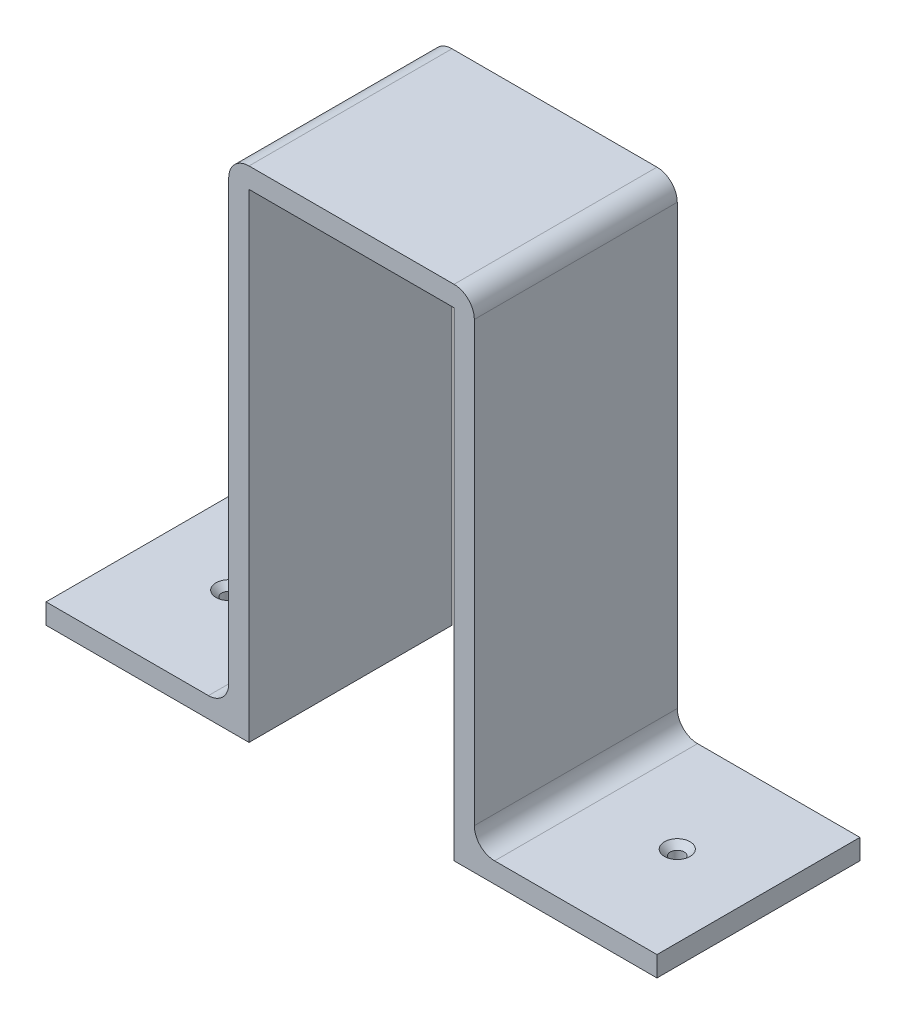
SolidWorks part; units mm, degrees
ref_plane "Plan de face" through (0, 0, 0) normal (0, 0, 1) x (1, 0, 0)
ref_plane "Plan de dessus" through (0, 0, 0) normal (0, 1, 0) x (1, 0, 0)
ref_plane "Plan de droite" through (0, 0, 0) normal (1, 0, 0) x (0, 0, -1)
sketch "Esquisse1" plane through (0, 0, 0) normal (0, 0, 1) x (1, 0, 0)
  line L0 (-25.25, 0) -> (25.25, 0)
  line L1 (-25.25, 0) -> (-25.25, -118)
  line L2 (-25.25, -118) -> (-75.25, -118)
  line L3 (0, -55) -> (0, 55) construction
  line L4 (25.25, 0) -> (25.25, -118)
  line L5 (25.25, -118) -> (75.25, -118)
  line L6 (-30.25, -113) -> (-75.25, -113)
  line L7 (-30.25, 5) -> (-30.25, -113)
  line L8 (-30.25, 5) -> (30.25, 5)
  line L9 (30.25, 5) -> (30.25, -113)
  line L10 (30.25, -113) -> (75.25, -113)
  line L11 (-75.25, -118) -> (-75.25, -113)
  line L12 (75.25, -118) -> (75.25, -113)
  point P4 (0, 0)
  dimension "D1" = 50.5
  dimension "D2" = 118
  dimension "D4" = 50
  dimension "D3" = 5
extrude "Boss.-Extru.1" add sketch "Esquisse1" along normal blind 50
fillet "Congé1" radius 5 4 edges at (30.25, -113, 25) (30.25, 5, 25) (-30.25, 5, 25) (-30.25, -113, 25)
hole_wizard "Fraisage pour vis à tête fraisée M31" positions "Esquisse2" profile "Esquisse3" countersink size "M3" standard "Ansi Metric" end condition through all
sketch "Esquisse2" plane through (0, -113, 0) normal (0, 1, 0) x (1, 0, 0)
  point P0 (-55.25, -25)
  point P2 (55.25, -25)
  point P4 (-55.1498, -15)
  point P5 (55.25, -25)
  point P6 (-55.25, -25)
sketch "Esquisse3" plane through (-55.25, -113, 25) normal (1, 0, 0) x (0, 0, 1)
  line L0 (0, 0) -> (0, 5)
  line L1 (0, 5) -> (1.7, 5)
  line L2 (1.7, 5) -> (1.7, 1.45)
  line L3 (1.7, 1.45) -> (3.15, 0)
  line L5 (3.15, 0) -> (0, 0)
  line L6 (-1.7, 1.45) -> (-3.15, 0) construction
  line L11 (0, -6.35) -> (0, 107.95) construction
  dimension "Diamètre du perçage jusqu'au prochain" = 3.4
  dimension "Profondeur du perçage jusqu'au prochain" = 5
  dimension "Diamètre du fraisage entrant" = 6.3
  dimension "Angle du fraisage entrant" = 90
